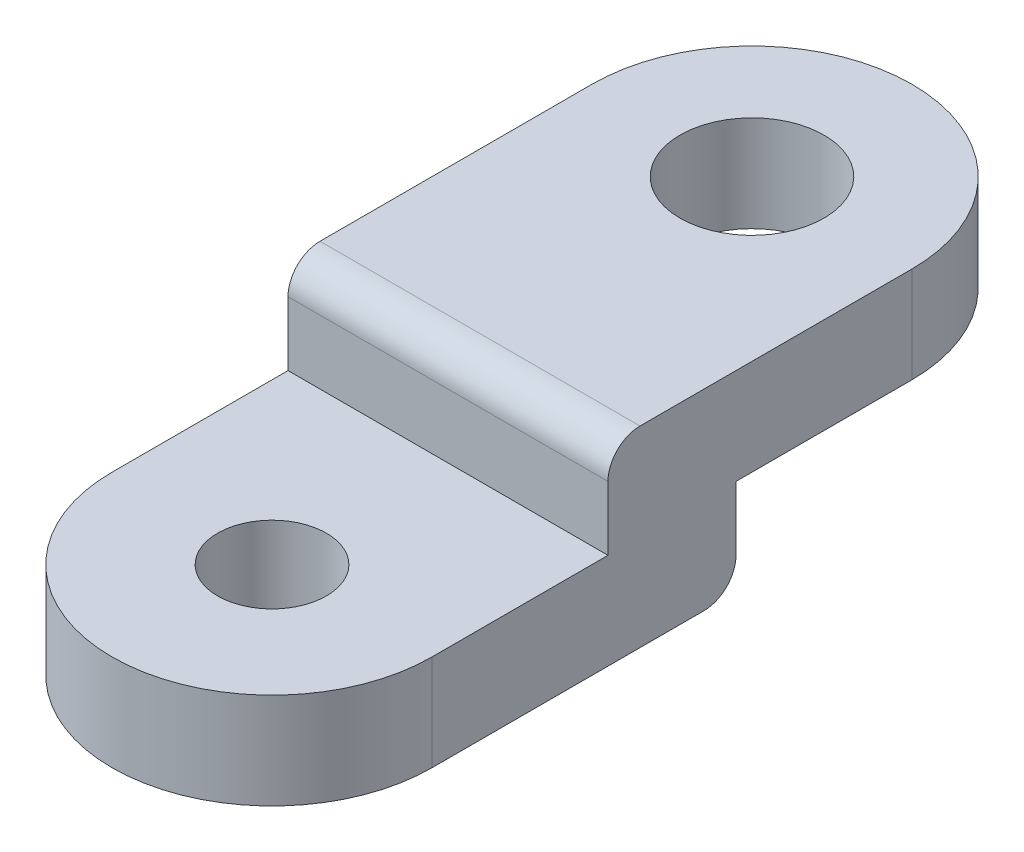
SolidWorks part; units mm, degrees
ref_plane "Plan de face" through (0, 0, 0) normal (0, 0, 1) x (1, 0, 0)
ref_plane "Plan de dessus" through (0, 0, 0) normal (0, 1, 0) x (1, 0, 0)
ref_plane "Plan de droite" through (0, 0, 0) normal (1, 0, 0) x (0, 0, -1)
sketch "Esquisse1" plane through (0, 0, 0) normal (0, 1, 0) x (1, 0, 0)
  line L0 (0, 0) -> (0, 30)
  line L1 (20, 30) -> (20, 0)
  arc A0 (20, 30) -> (0, 30) centre (10, 30) ccw
  arc A1 (0, 0) -> (20, 0) centre (10, 0) ccw
  dimension "D1" = 20
  dimension "D2" = 30
extrude "Boss.-Extru.1" add sketch "Esquisse1" along normal blind 6
sketch "Esquisse7" plane through (0, 6, 0) normal (0, 1, 0) x (1, 0, 0)
  arc A0 (20, 30) -> (0, 30) centre (10, 30) ccw construction
  arc A1 (0, 0) -> (20, 0) centre (10, 0) ccw construction
  point P0 (10, 30)
  point P5 (10, 0)
sketch "Esquisse12" plane through (0, 0, 0) normal (0, -1, 0) x (1, 0, 0)
  line L0 (0, -30) -> (20, -30)
  line L1 (0, -30) -> (0, 0) construction
  line L2 (20, 0) -> (20, -30) construction
  line L3 (20, -30) -> (20, 0)
  line L4 (0, 0) -> (0, -30)
  arc A0 (20, 0) -> (0, 0) centre (10, 0) ccw construction
  arc A1 (20, 0) -> (0, 0) centre (10, 0) ccw
extrude "Boss.-Extru.2" add sketch "Esquisse12" along normal blind 12
sketch "Esquisse14" plane through (20, 0, 0) normal (1, 0, 0) x (0, 0, -1)
  line L0 (11, 6) -> (11, 0)
  line L1 (0, 6) -> (30, 6) construction
  line L2 (11, 0) -> (-10, 0)
  line L3 (-10, 6) -> (-10, -12) construction
  line L4 (-10, 0) -> (-10, 6)
  line L5 (-10, 6) -> (11, 6)
  line L6 (30, 0) -> (40, 0) construction
  line L7 (15, 10.1399) -> (15, -19.2589) construction
  line L10 (0, 6) -> (0, -12) construction
  line L11 (30, 6) -> (30, 0) construction
  line L12 (30, 0) -> (19, 0)
  line L13 (19, 0) -> (19, -6)
  line L14 (19, -6) -> (-10, -6)
  line L15 (-10, -6) -> (-10, -12)
  line L16 (-10, -12) -> (0, -12) construction
  line L17 (-10, -12) -> (30, -12)
  line L18 (30, -12) -> (30, 0)
  dimension "D1" = 4
  dimension "D2" = 6
  dimension "D3" = 8
extrude "Enlèv. mat.-Extru.2" cut sketch "Esquisse14" against normal through all
hole_wizard "Dégagement M81" positions "Esquisse15" profile "Esquisse16" hole size "M8" standard "ISO" end condition through all
sketch "Esquisse15" plane through (0, 6, 0) normal (0, 1, 0) x (1, 0, 0)
  point P0 (10, 30)
sketch "Esquisse16" plane through (10, 6, -30) normal (1, 0, 0) x (0, 0, 1)
  line L0 (0, 0) -> (0, 12)
  line L1 (0, 12) -> (4.5, 12)
  line L2 (4.5, 12) -> (4.5, 0)
  line L5 (4.5, 0) -> (0, 0)
  line L11 (0, -6.35) -> (0, 107.95) construction
  dimension "Diamètre du perçage jusqu'au prochain" = 9
  dimension "Profondeur du perçage jusqu'au prochain" = 12
hole_wizard "Trou taraudé M82" positions "Esquisse17" profile "Esquisse18" tap size "M8" standard "ISO" end condition through all
sketch "Esquisse17" plane through (0, 0, 0) normal (0, 1, 0) x (1, 0, 0)
  arc A0 (0, 0) -> (20, 0) centre (10, 0) ccw construction
  point P0 (10, 0)
cosmetic thread "Filetage de perçage13" parameters "D2"=8
sketch "Esquisse18" plane through (10, 0, 0) normal (1, 0, 0) x (0, 0, 1)
  line L0 (0, 0) -> (0, 6)
  line L1 (0, 6) -> (3.4, 6)
  line L2 (3.4, 6) -> (3.4, 0)
  line L5 (3.4, 0) -> (0, 0)
  line L11 (0, -6.35) -> (0, 107.95) construction
  dimension "Diamètre du trou pour taraudage jusqu'au prochain" = 6.8
  dimension "Profondeur du trou pour taraudage jusqu'au prochain" = 6
fillet "Congé1" radius 2 2 edges at (10, 6, -11) (10, -6, -19)
